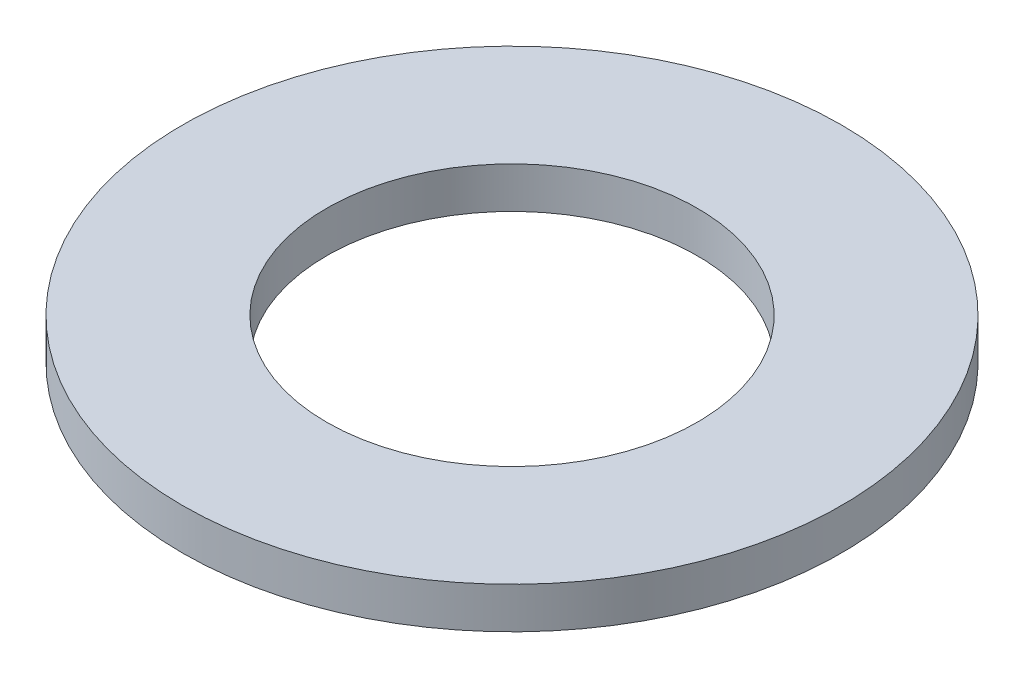
SolidWorks part; units mm, degrees
material "AISI 304"
ref_plane "Alzado" through (0, 0, 0) normal (0, 0, 1) x (1, 0, 0)
ref_plane "Planta" through (0, 0, 0) normal (0, 1, 0) x (1, 0, 0)
ref_plane "Vista lateral" through (0, 0, 0) normal (1, 0, 0) x (0, 0, -1)
sketch "Croquis1" plane through (0, 0, 0) normal (0, 1, 0) x (1, 0, 0)
  circle A0 centre (0, 0) radius 8
  circle A1 centre (0, 0) radius 4.5
  dimension "D1" = 16
  dimension "D2" = 9
extrude "Saliente-Extruir1" add sketch "Croquis1" along normal blind 1
